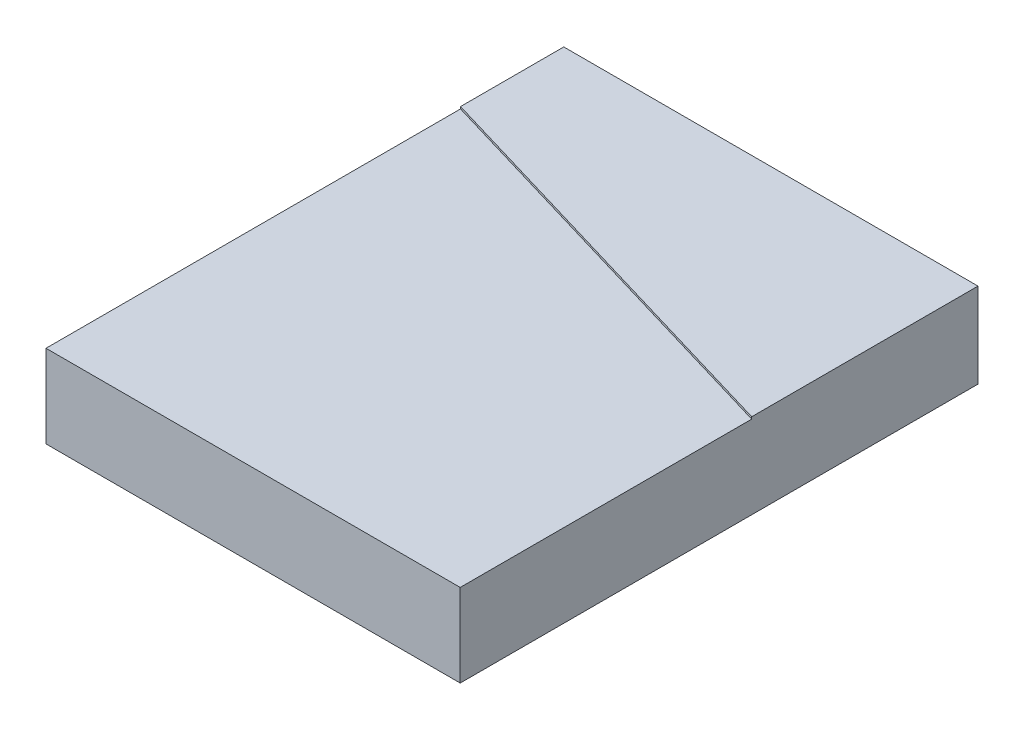
SolidWorks part; units mm, degrees
ref_plane "Front" through (0, 0, 0) normal (0, 0, 1) x (1, 0, 0)
ref_plane "Top" through (0, 0, 0) normal (0, 1, 0) x (1, 0, 0)
ref_plane "Right" through (0, 0, 0) normal (1, 0, 0) x (0, 0, -1)
sketch "Эскиз1" plane through (0, 0, 0) normal (0, 1, 0) x (1, 0, 0)
  line L0 (-10, 12.5) -> (10, 12.5)
  line L1 (-10, 12.5) -> (-10, -12.5)
  line L2 (10, 12.5) -> (10, -12.5)
  line L3 (-10, -12.5) -> (10, -12.5)
  line L4 (-10, 12.5) -> (10, -12.5) construction
  line L5 (10, 12.5) -> (-10, -12.5) construction
  point P1 (0, 0)
extrude "Бобышка-Вытянуть1" add sketch "Эскиз1" along normal blind 4
sketch "Эскиз2" plane through (0, 4, 0) normal (0, 1, 0) x (1, 0, 0)
  line L0 (-10, 12.5) -> (-10, 7.5146)
  line L1 (-10, 12.5) -> (-10, -12.5) construction
  line L2 (-10, 7.5146) -> (10, 1.5745)
  line L3 (10, -12.5) -> (10, 12.5) construction
  line L4 (10, 1.5745) -> (10, 12.5)
  line L5 (10, 12.5) -> (-10, 12.5)
extrude "Бобышка-Вытянуть2" add sketch "Эскиз2" along normal blind 0.1
